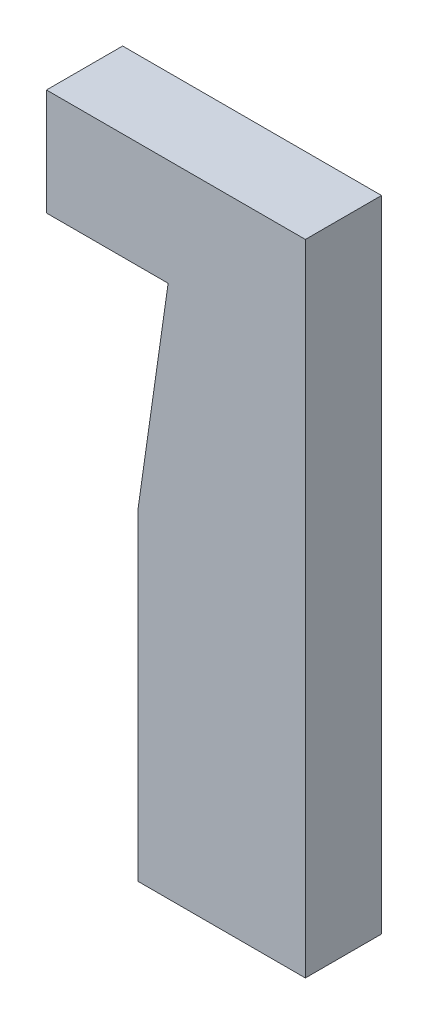
SolidWorks part; units mm, degrees
ref_plane "Front Plane" through (0, 0, 0) normal (0, 0, 1) x (1, 0, 0)
ref_plane "Top Plane" through (0, 0, 0) normal (0, 1, 0) x (1, 0, 0)
ref_plane "Right Plane" through (0, 0, 0) normal (1, 0, 0) x (0, 0, -1)
sketch "Sketch2" plane through (0, 0, 0) normal (0, 0, 1) x (1, 0, 0)
  line L1 (0, 0) -> (-13.97, 0)
  line L2 (0, 0) -> (0, 53.34)
  line L3 (0, 53.34) -> (-13.97, 53.34)
  line L4 (-13.97, 0) -> (-13.97, 53.34)
  line L5 (0, 53.34) -> (-21.59, 53.34)
  line L6 (0, 53.34) -> (0, 44.45)
  line L7 (0, 44.45) -> (-21.59, 44.45)
  line L8 (-21.59, 53.34) -> (-21.59, 44.45)
  dimension "D1" = 13.97
  dimension "D2" = 53.34
  dimension "D3" = 8.89
  dimension "D4" = 21.59
extrude "Boss-Extrude1" add sketch "Sketch2" along normal blind 6.35 contours L5 L8 L7 L4 | L7 L2 L3 L4 | L2 L7 L4 L1
sketch "Sketch3" plane through (0, 0, 0) normal (0, 0, -1) x (-1, 0, 0)
  line L0 (0, 0) -> (13.97, 0) construction
  line L1 (13.97, 0) -> (13.97, 44.45) construction
  circle A0 centre (6.985, 15.24) radius 4.0005
  dimension "D3" = 8.001
  dimension "D1" = 15.24
  dimension "D2" = 6.985
extrude "Cut-Extrude1" cut sketch "Sketch3" against normal blind 2.794
sketch "Sketch4" plane through (0, 0, 0) normal (0, 0, -1) x (-1, 0, 0)
  line L0 (13.97, 0) -> (13.97, 44.45) construction
  line L4 (6.985, 29.718) -> (9.017, 29.718)
  line L5 (9.017, 15.24) -> (9.017, 29.718)
  line L8 (6.985, 29.718) -> (4.953, 29.718)
  line L9 (4.953, 15.24) -> (4.953, 29.718)
  line L10 (4.953, 15.24) -> (4.953, 0.762)
  line L11 (9.017, 15.24) -> (9.017, 0.762)
  line L12 (4.953, 0.762) -> (9.017, 0.762)
  dimension "D1" = 28.956
  dimension "D2" = 4.953
  dimension "D3" = 9.017
extrude "Cut-Extrude2" cut sketch "Sketch4" against normal blind 1.5875
sketch "Sketch5" plane through (0, 0, 0) normal (0, 0, -1) x (-1, 0, 0)
  line L0 (13.97, 44.45) -> (11.4443, 44.45)
  line L5 (11.4443, 44.45) -> (13.97, 26.7917)
  line L6 (13.97, 0) -> (13.97, 44.45) construction
  line L7 (13.97, 26.7917) -> (13.97, 44.45)
extrude "Cut-Extrude3" cut sketch "Sketch5" against normal through all
